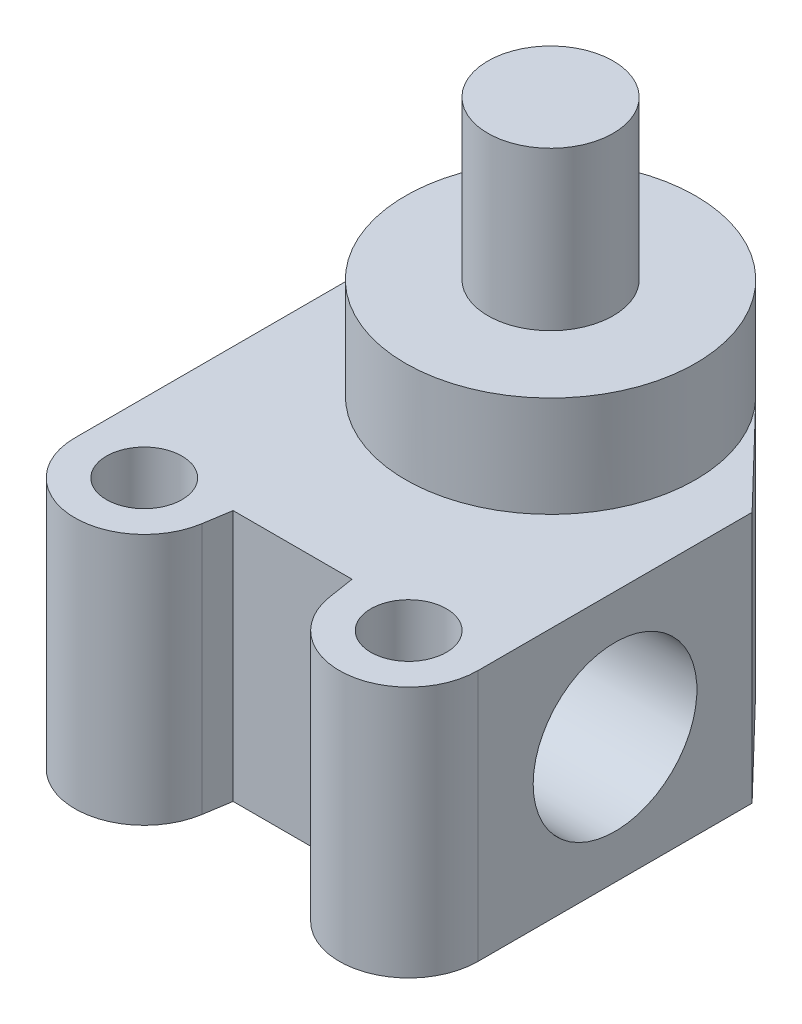
SolidWorks part; units mm, degrees
ref_plane "Front Plane" through (0, 0, 0) normal (0, 0, 1) x (1, 0, 0)
ref_plane "Top Plane" through (0, 0, 0) normal (0, 1, 0) x (1, 0, 0)
ref_plane "Right Plane" through (0, 0, 0) normal (1, 0, 0) x (0, 0, -1)
sketch "Sketch1" plane through (0, 0, 0) normal (0, 1, 0) x (1, 0, 0)
  line L0 (-7.493, -32.512) -> (7.493, -32.512)
  line L1 (-25.4, 0) -> (-25.4, -34.544)
  line L2 (25.4, 0) -> (25.4, -34.544)
  line L3 (-25.4, 0) -> (-13.1674, 12.6914)
  line L4 (13.1674, 12.6914) -> (25.4, 0)
  line L5 (-16.6624, -34.544) -> (16.6624, -34.544) construction
  line L6 (-8.0328, -35.9135) -> (-7.493, -32.512)
  line L7 (8.0328, -35.9135) -> (7.493, -32.512)
  arc A0 (-13.1674, 12.6914) -> (13.1674, 12.6914) centre (0, 0) cw
  circle A1 centre (16.6624, -34.544) radius 4.7625
  circle A2 centre (-16.6624, -34.544) radius 4.7625
  arc A3 (-25.4, -34.544) -> (-8.0328, -35.9135) centre (-16.6624, -34.544) ccw
  arc A4 (8.0328, -35.9135) -> (25.4, -34.544) centre (16.6624, -34.544) ccw
  point P6 (0, -32.512)
  point P15 (0, 18.288)
  point P16 (0, -34.544)
  dimension "D1" = 50.8
  dimension "D4" = 9.525
  dimension "D6" = 18.288
  dimension "D2" = 14.986
  dimension "D3" = 34.544
  dimension "D5" = 50.8
  dimension "D7" = 33.3248
extrude "Body" add sketch "Sketch1" along normal blind 31.75
sketch "Sketch3" plane through (0, 0, 0) normal (0, -1, 0) x (1, 0, 0)
  circle A0 centre (0, 0) radius 18.288
  arc A1 (-13.1674, -12.6914) -> (13.1674, -12.6914) centre (0, 0) ccw construction
extrude "Pinion Carrier" add sketch "Sketch3" against normal blind 44.45
sketch "Sketch4" plane through (0, 0, 0) normal (0, -1, 0) x (1, 0, 0)
  circle A0 centre (0, 0) radius 7.8994
  dimension "D1" = 15.7988
extrude "Pinion" add sketch "Sketch4" against normal blind 64.3636
sketch "Sketch5" plane through (0, 0, 0) normal (0, -1, 0) x (1, 0, 0)
  circle A0 centre (0, 0) radius 12.7
  dimension "D1" = 25.4
extrude "Pinion Bottom" add sketch "Sketch5" along normal blind 5.8674
fillet "Pinion Bottom Fillet" radius 3.81 1 edges at (0, -5.8674, -12.7)
sketch "Sketch2" plane through (-25.4, 0, 0) normal (-1, 0, 0) x (0, 0, 1)
  line L0 (0, 31.75) -> (0, 0) construction
  line L1 (0, 0) -> (34.544, 0) construction
  circle A0 centre (17.272, 15.875) radius 10.3187
  point P4 (0, 15.875)
  point P7 (17.272, 0)
  dimension "D1" = 20.6375
extrude "Rack Hole" cut sketch "Sketch2" against normal through all
